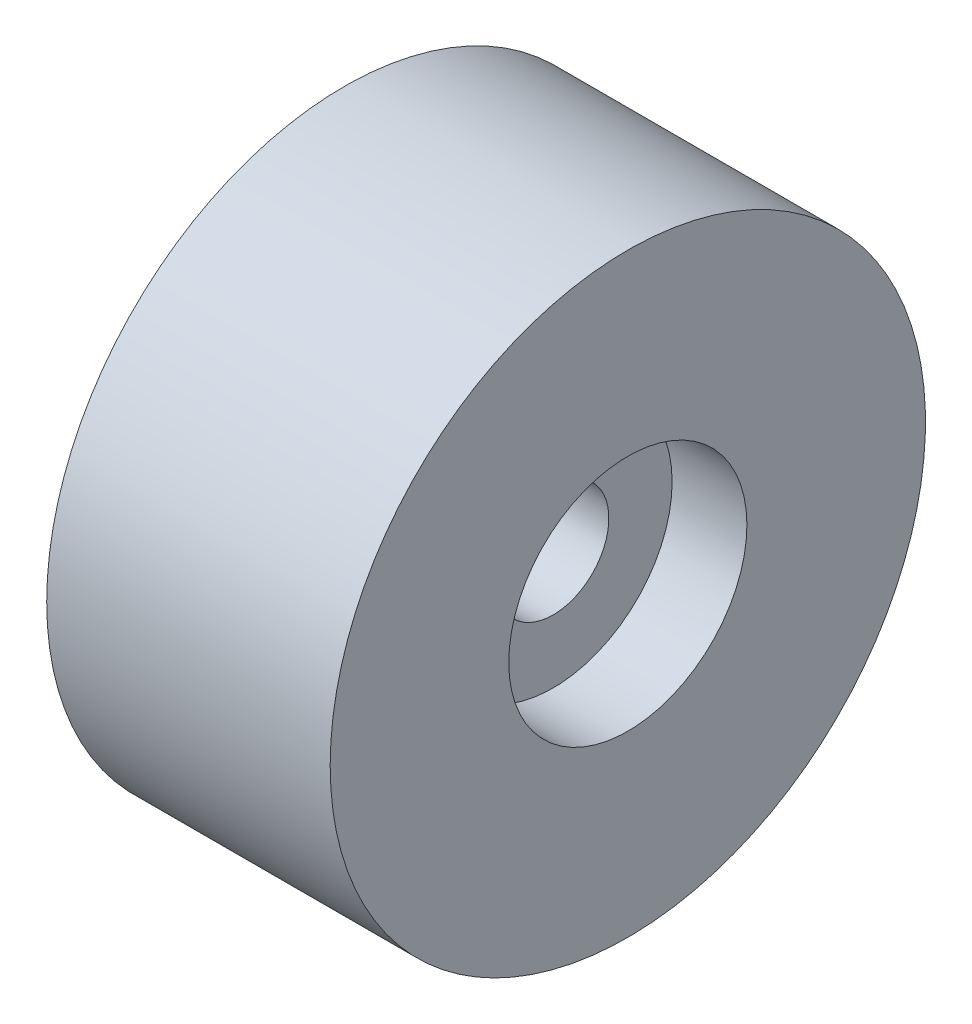
SolidWorks part; units mm, degrees
ref_plane "Front Plane" through (0, 0, 0) normal (0, 0, 1) x (1, 0, 0)
ref_plane "Top Plane" through (0, 0, 0) normal (0, 1, 0) x (1, 0, 0)
ref_plane "Right Plane" through (0, 0, 0) normal (1, 0, 0) x (0, 0, -1)
sketch "Sketch1" plane through (0, 0, 0) normal (0, 0, 1) x (1, 0, 0)
  line L0 (0, -25) -> (0, -133.35)
  line L1 (0, -133.35) -> (-63.5, -133.35)
  line L2 (-63.5, -133.35) -> (-63.5, -53.35)
  line L3 (-63.5, -53.35) -> (-30, -53.35)
  line L4 (-30, -53.35) -> (-30, -25)
  line L5 (-30, -25) -> (0, -25)
  line L6 (-62.8571, 0) -> (53.4694, 0) construction
  dimension "D1" = 25
  dimension "D2" = 133.35
  dimension "D3" = 80
  dimension "D4" = 63.5
  dimension "D5" = 30
revolve "Revolve1" add sketch "Sketch1" angle 360 about L6
mirror "Mirror1" about plane through (0, 0, 0) normal (1, 0, 0) of "Revolve1"
